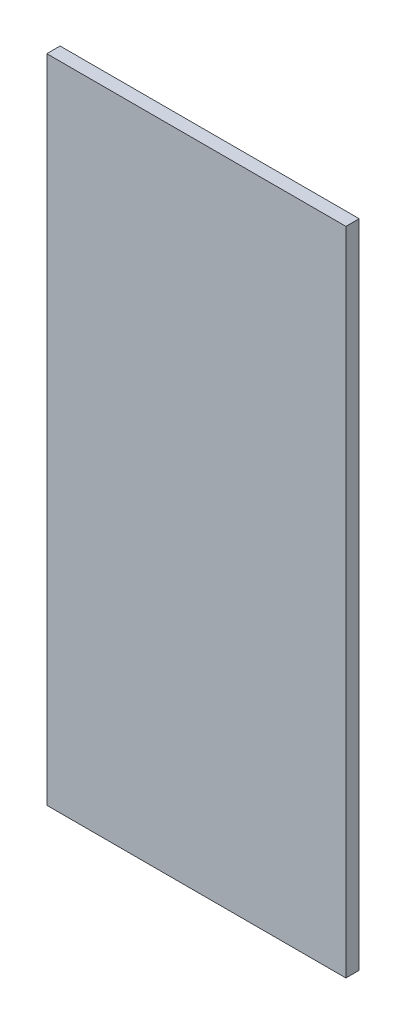
SolidWorks part; units mm, degrees
ref_plane "Front Plane" through (0, 0, 0) normal (0, 0, 1) x (1, 0, 0)
ref_plane "Top Plane" through (0, 0, 0) normal (0, 1, 0) x (1, 0, 0)
ref_plane "Right Plane" through (0, 0, 0) normal (1, 0, 0) x (0, 0, -1)
ref_plane "Plane1" through (0, 0, 0) normal (0, 0, 1) x (1, 0, 0)
sketch "Sketch1" plane through (0, 0, 0) normal (0, 0, 1) x (1, 0, 0)
  line L1 (70.95, 199.0793) -> (-19.05, 199.0793)
  line L2 (70.95, 199.0793) -> (70.95, 394.95)
  line L3 (70.95, 394.95) -> (-19.05, 394.95)
  line L4 (-19.05, 199.0793) -> (-19.05, 394.95)
  line L8 (-19.05, 592.2961) -> (-19.05, -17.3039) construction
  line L51 (-30.4931, 211.9542) -> (-11.4606, 203.0793)
  line L52 (52.974, 390.95) -> (-30.4931, 211.9542)
  line L53 (72.0065, 382.075) -> (52.974, 390.95)
  line L54 (-11.4606, 203.0793) -> (72.0065, 382.075)
  line L55 (-30.4931, 211.9542) -> (-11.4606, 203.0793) construction
  line L56 (52.974, 390.95) -> (-30.4931, 211.9542) construction
  line L57 (72.0065, 382.075) -> (52.974, 390.95) construction
  line L58 (-11.4606, 203.0793) -> (72.0065, 382.075) construction
  point P4 (-24.5254, -205.955)
  point P5 (75.0063, 38.9801)
  point P6 (-35.3009, -173.2162)
  point P7 (0, 0)
  dimension "D1" = 4
  dimension "D2" = 4
  dimension "D4" = 90
  dimension "D5" = 0
extrude "Boss-Extrude1" add sketch "Sketch1" along normal blind 4
